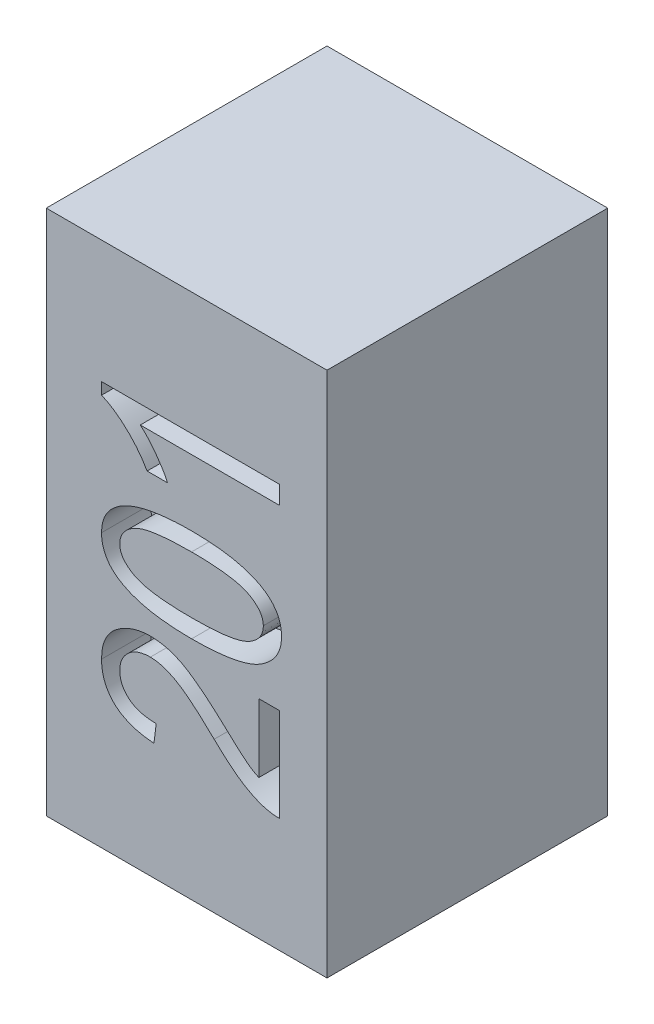
SolidWorks part; units mm, degrees
ref_plane "Plan de face" through (0, 0, 0) normal (0, 0, 1) x (1, 0, 0)
ref_plane "Plan de dessus" through (0, 0, 0) normal (0, 1, 0) x (1, 0, 0)
ref_plane "Plan de droite" through (0, 0, 0) normal (1, 0, 0) x (0, 0, -1)
sketch "Esquisse1" plane through (0, 0, 0) normal (0, 0, 1) x (1, 0, 0)
  line L0 (-1.3836, 0) -> (1.5164, 0) construction
  line L1 (0, 1.23) -> (0, -1.03) construction
  line L3 (-0.4, 0.75) -> (0.4, 0.75)
  line L4 (-0.4, 0.75) -> (-0.4, -0.75)
  line L5 (-0.4, -0.75) -> (0.4, -0.75)
  line L6 (0.4, 0.75) -> (0.4, -0.75)
  dimension "D1" = 1.5
  dimension "D2" = 0.8
extrude "Boss.-Extru.1" add sketch "Esquisse1" along normal blind 0.8
sketch "Esquisse2" plane through (0, 0, 0.8) normal (0, 0, 1) x (1, 0, 0)
  line L0 (0.264, -0.45) -> (0.264, 0.3069) construction
  line L1 (0.4, -0.75) -> (0.4, 0.75) construction
  line L2 (-0.4, -0.75) -> (0.4, -0.75) construction
  text T0 "201" font "Arial Narrow" height 0.5
  point P3 (0.2538, 0.3069)
  dimension "D1" = 0.136
  dimension "D2" = 0.3
extrude "Enlèv. mat.-Extru.1" cut sketch "Esquisse2" against normal blind 0.14
